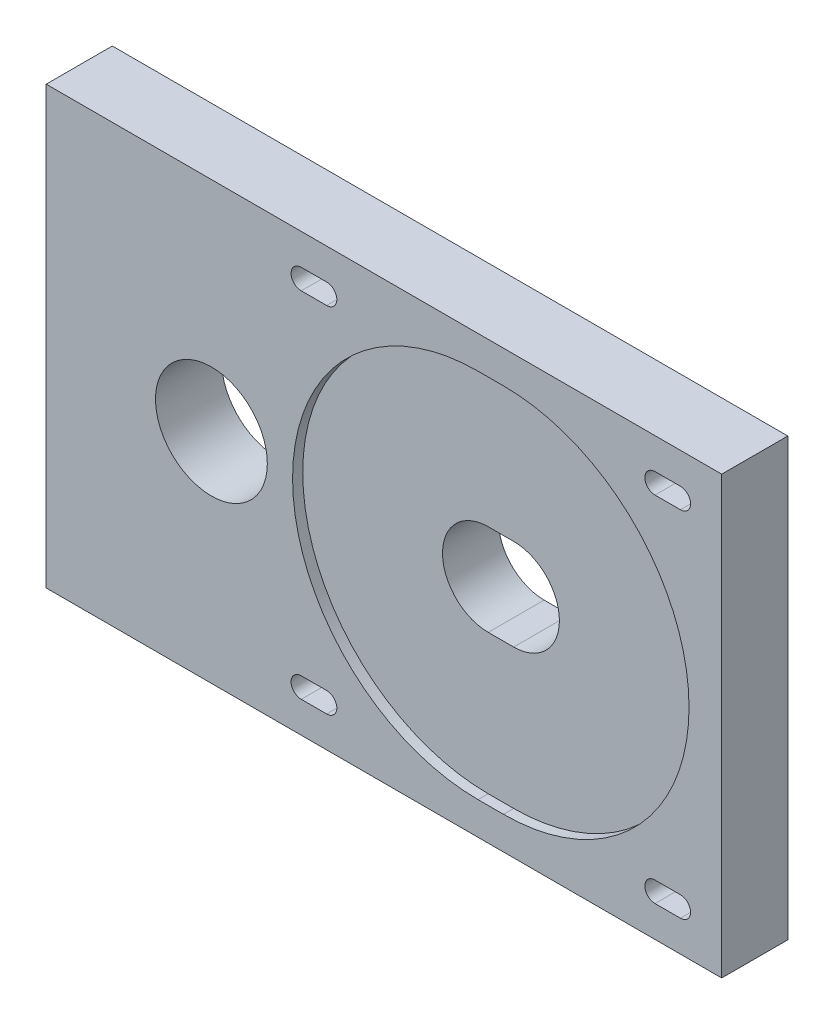
SolidWorks part; units mm, degrees
ref_plane "Płaszczyzna przednia" through (0, 0, 0) normal (0, 0, 1) x (1, 0, 0)
ref_plane "Płaszczyzna górna" through (0, 0, 0) normal (0, 1, 0) x (1, 0, 0)
ref_plane "Płaszczyzna prawa" through (0, 0, 0) normal (1, 0, 0) x (0, 0, -1)
sketch "Szkic1" plane through (0, 0, 0) normal (0, 0, 1) x (1, 0, 0)
  line L5 (66.45, -42.925) -> (-66.45, -42.925)
  line L6 (66.45, -42.925) -> (66.45, 42.925)
  line L7 (66.45, 42.925) -> (-66.45, 42.925)
  line L8 (-66.45, -42.925) -> (-66.45, 42.925)
  line L9 (66.45, -42.925) -> (-66.45, 42.925) construction
  line L10 (66.45, 42.925) -> (-66.45, -42.925) construction
  point P0 (0, 0)
  dimension "D1" = 132.9
  dimension "D2" = 85.85
extrude "Dodanie-wyciągnięcie1" add sketch "Szkic1" along normal blind 13
sketch "Szkic2" plane through (0, 0, 13) normal (0, 0, 1) x (1, 0, 0)
  line L0 (-66.45, 42.925) -> (-66.45, -42.925) construction
  line L1 (66.45, -42.925) -> (66.45, 42.925) construction
  line L2 (-66.45, -42.925) -> (-66.45, 42.925) construction
  line L3 (-66.45, -42.925) -> (66.45, -42.925) construction
  line L8 (23.52, -36.5) -> (18.52, -36.5)
  line L9 (23.52, -36.5) -> (23.52, 36.5)
  line L10 (23.52, 36.5) -> (18.52, 36.5)
  line L11 (18.52, -36.5) -> (18.52, 36.5)
  line L12 (66.45, 42.925) -> (-66.45, 42.925) construction
  circle A0 centre (23.52, 0) radius 36.5
  circle A1 centre (18.52, 0) radius 36.5
  dimension "D1" = 89.97
  dimension "D3" = 84.97
  dimension "D4" = 73
  dimension "D5" = 73
  dimension "D7" = 6.425
  dimension "D2" = 42.93
  dimension "D6" = 6.425
extrude "Wytnij-wyciągnięcie1" cut sketch "Szkic2" against normal blind 2 contours L11 A0 | L9 A1 | A1 L9 A0 | L11 A1 A0
sketch "Szkic3" plane through (0, 0, 13) normal (0, 0, 1) x (1, 0, 0)
  line L0 (66.45, 42.925) -> (-66.45, 42.925) construction
  line L1 (66.45, -42.925) -> (66.45, 42.925) construction
  line L3 (53.325, 36.8) -> (58.325, 36.8)
  line L4 (53.325, 36.8) -> (53.325, 32.8)
  line L5 (53.325, 32.8) -> (58.325, 32.8)
  line L6 (58.325, 36.8) -> (58.325, 32.8)
  circle A0 centre (58.325, 34.8) radius 2
  circle A1 centre (53.325, 34.8) radius 2
  dimension "D1" = 8.125
  dimension "D3" = 5
  dimension "D4" = 4
  dimension "D5" = 4
  dimension "D2" = 8.125
  dimension "D6" = 5
extrude "Wytnij-wyciągnięcie3" cut sketch "Szkic3" against normal blind 13 contours L4 A1 | L4 A1 | A1 L5 A0 L3 | L6 A0 | L6 A0
pattern_linear "Szyk liniowy1" count 2 spacing 69.6 along (0, -1, 0) count 2 spacing 69.6 along (-1, 0, 0) of "Wytnij-wyciągnięcie3"
sketch "Szkic6" plane through (0, 0, 13) normal (0, 0, 1) x (1, 0, 0)
  line L1 (18.52, 9) -> (23.52, 9)
  line L2 (18.52, 9) -> (18.52, -9)
  line L3 (18.52, -9) -> (23.52, -9)
  line L4 (23.52, 9) -> (23.52, -9)
  circle A0 centre (23.52, 0) radius 9
  circle A1 centre (18.52, 0) radius 9
  dimension "D1" = 18
  dimension "D2" = 18
extrude "Wytnij-wyciągnięcie4" cut sketch "Szkic6" against normal blind 13 contours L2 A1 A0 | L2 A0 | L4 A1 A0 L2 | L4 A1 | A1 L4 A0 | A1 L3 A0 | A1 A0 L4 | L2 A1 A0 | A1 A0 L1 | A0 A1 L2 | A1 L4 A0
sketch "Szkic7" plane through (0, 0, 13) normal (0, 0, 1) x (1, 0, 0)
  line L0 (-66.45, 42.925) -> (-66.45, -42.925) construction
  circle A0 centre (-33.95, 0) radius 11
  point P4 (0, 0)
  point P8 (0, 0)
  dimension "D1" = 32.5
  dimension "D2" = 22
extrude "Wytnij-wyciągnięcie5" cut sketch "Szkic7" against normal blind 13
sketch "Szkic8" plane through (-66.45, 0, 0) normal (-1, 0, 0) x (0, 0, 1)
  line L0 (0, 42.925) -> (0, -42.925) construction
  line L2 (13, 42.925) -> (0, 42.925) construction
  line L4 (13, -42.925) -> (0, -42.925) construction
  circle A0 centre (6.5, 34.925) radius 3
  circle A1 centre (6.5, -34.925) radius 3
  dimension "D1" = 6.5
  dimension "D3" = 8
  dimension "D4" = 6
  dimension "D5" = 6
  dimension "D2" = 8
  dimension "D6" = 6.5
extrude "Wytnij-wyciągnięcie6" cut sketch "Szkic8" against normal blind 25
